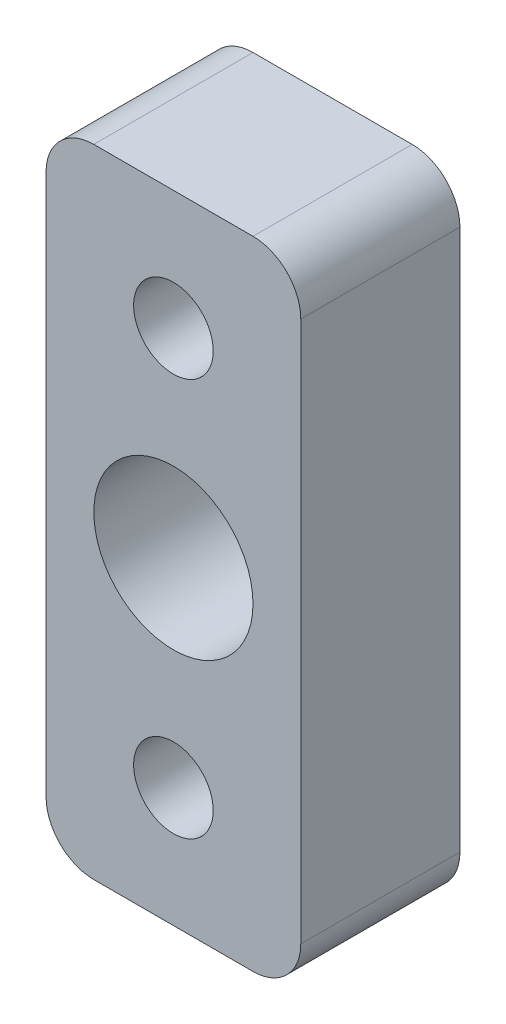
SolidWorks part; units mm, degrees
material "瞎编数据的PLA"
ref_plane "前视基准面" through (0, 0, 0) normal (0, 0, 1) x (1, 0, 0)
ref_plane "上视基准面" through (0, 0, 0) normal (0, 1, 0) x (1, 0, 0)
ref_plane "右视基准面" through (0, 0, 0) normal (1, 0, 0) x (0, 0, -1)
sketch "草图1" plane through (0, 0, 0) normal (0, 0, 1) x (1, 0, 0)
  line L0 (0, 0) -> (0, 25) construction
  line L2 (-8, 32.5) -> (8, 32.5)
  line L3 (-8, 32.5) -> (-8, -7.5)
  line L4 (-8, -7.5) -> (8, -7.5)
  line L5 (8, 32.5) -> (8, -7.5)
  line L6 (-8, 32.5) -> (8, -7.5) construction
  line L7 (-8, -7.5) -> (8, 32.5) construction
  circle A0 centre (0, 25) radius 2.5
  circle A1 centre (0, 0) radius 2.5
  circle A2 centre (0, 12.5) radius 5
  point P5 (0, 12.5)
  dimension "D1" = 5
  dimension "D5" = 10
  dimension "D2" = 25
  dimension "D3" = 16
  dimension "D4" = 40
extrude "凸台-拉伸1" add sketch "草图1" along normal blind 10
fillet "圆角1" radius 3 4 edges at (8, 32.5, 5) (-8, 32.5, 5) (-8, -7.5, 5) (8, -7.5, 5)
